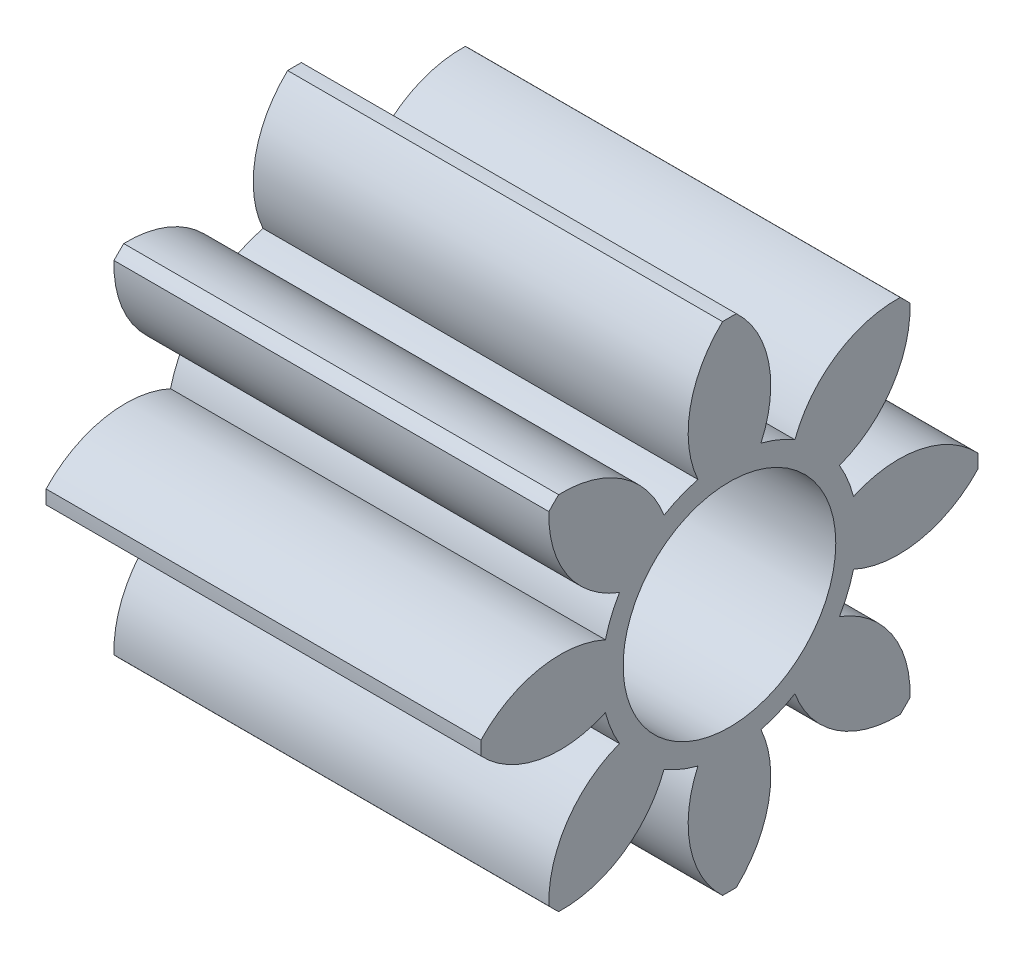
SolidWorks part; units mm, degrees
ref_plane "Front Plane" through (0, 0, 0) normal (0, 0, 1) x (1, 0, 0)
ref_plane "Top Plane" through (0, 0, 0) normal (0, 1, 0) x (1, 0, 0)
ref_plane "Right Plane" through (0, 0, 0) normal (1, 0, 0) x (0, 0, -1)
sketch "Sketch1" plane through (0, 0, 0) normal (1, 0, 0) x (0, 0, -1)
  circle A0 centre (0, 0) radius 2.286
  circle A1 centre (0, 0) radius 0.9779
  dimension "D1" = 1.9558
  dimension "D2" = 4.572
extrude "Boss-Extrude1" add sketch "Sketch1" along normal blind 4
sketch "Sketch2" plane through (4, 0, 0) normal (1, 0, 0) x (0, 0, -1)
  line L0 (0, 0) -> (-4.0353, 0) construction
  line L1 (-1.1409, 0.2899) -> (-1.1409, -0.2899) construction
  line L2 (0, 0) -> (-1.1409, 0.2899) construction
  line L3 (0, 0) -> (0, 1.0451) construction
  line L4 (0, 0) -> (-2.4247, 1.0044) construction
  arc A0 (-1.1409, 0.2899) -> (-2.3826, -0.0583) centre (-1.5554, -0.6202) ccw
  arc A3 (-1.0117, 0.6018) -> (-1.1409, 0.2899) centre (0, 0) ccw
  arc A4 (-1.0117, 0.6018) -> (-1.6435, 1.726) centre (-0.6613, 1.5384) cw
  arc A5 (-1.6435, 1.726) -> (-2.3826, -0.0583) centre (0, 0) ccw
  dimension "D1" = 22.5
  dimension "D2" = 2.3833
extrude "Cut-Extrude1" cut sketch "Sketch2" against normal through all
pattern_circular "CirPattern1" count 8 over 360 about axis through (0, 0, 0) along (1, 0, 0) of "Cut-Extrude1"
